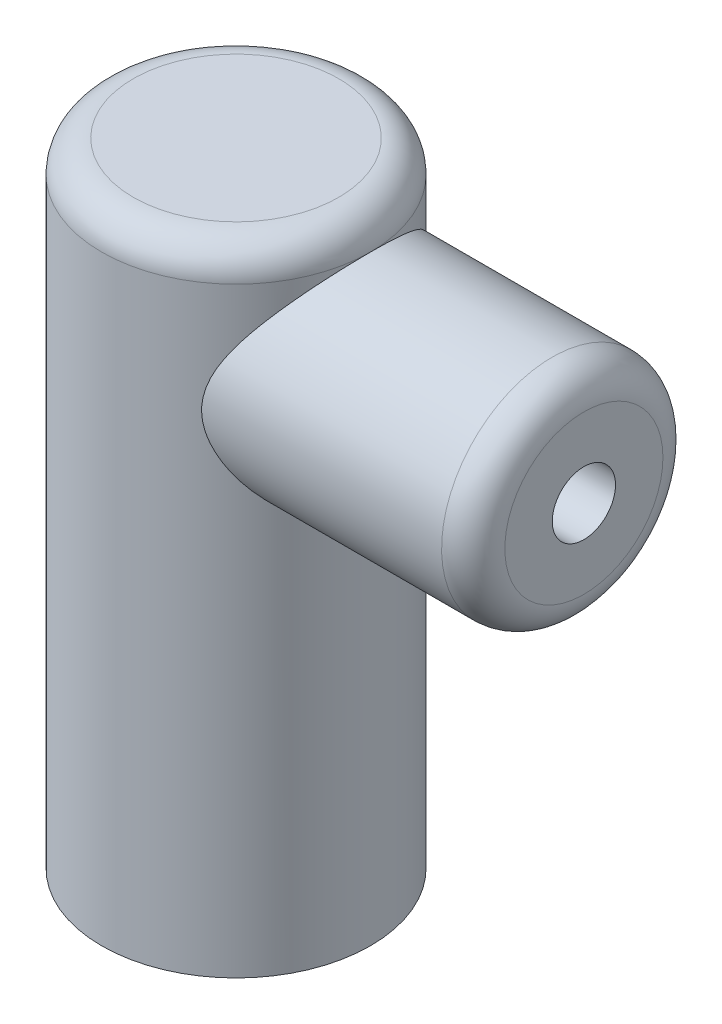
SolidWorks part; units mm, degrees
ref_plane "Front Plane" through (0, 0, 0) normal (0, 0, 1) x (1, 0, 0)
ref_plane "Top Plane" through (0, 0, 0) normal (0, 1, 0) x (1, 0, 0)
ref_plane "Right Plane" through (0, 0, 0) normal (1, 0, 0) x (0, 0, -1)
sketch "Sketch1" plane through (0, 0, 0) normal (0, 1, 0) x (1, 0, 0)
  circle A0 centre (0, 0) radius 42.5
  dimension "D1" = 85
extrude "Boss-Extrude1" add sketch "Sketch1" along normal blind 200
sketch "Sketch2" plane through (0, 0, 0) normal (1, 0, 0) x (0, 0, -1)
  line L0 (0, 200) -> (0, 155) construction
  line L1 (42.5, 200) -> (-42.5, 200) construction
  circle A0 centre (0, 155) radius 35
  dimension "D2" = 70
  dimension "D1" = 45
extrude "Boss-Extrude2" add sketch "Sketch2" along normal blind 110
fillet "Fillet1" radius 10 1 edges at (0, 200, 42.5)
sketch "Sketch3" plane through (110, 0, 0) normal (1, 0, 0) x (0, 0, -1)
  circle A0 centre (0, 155) radius 10
  dimension "D1" = 20
extrude "Cut-Extrude1" cut sketch "Sketch3" against normal blind 40 contours A0
fillet "Fillet2" radius 10 1 edges at (110, 155, -35)
